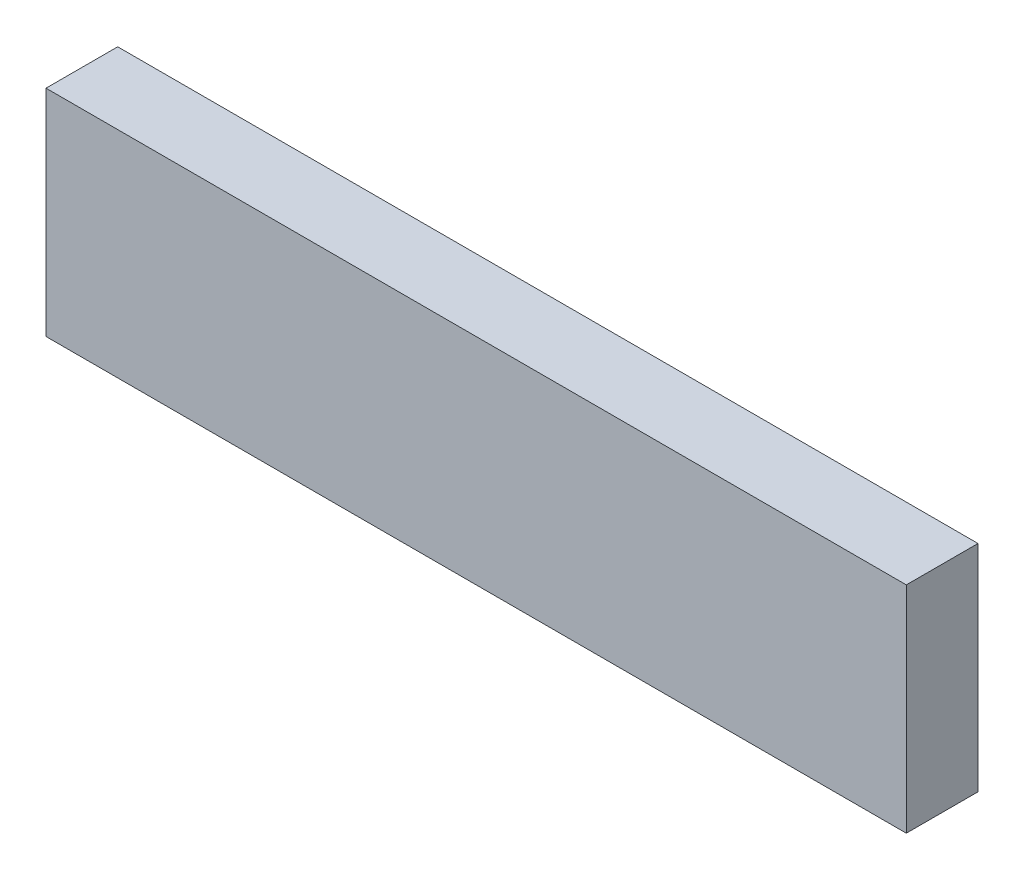
SolidWorks part; units mm, degrees
ref_plane "Front Plane" through (0, 0, 0) normal (0, 0, 1) x (1, 0, 0)
ref_plane "Top Plane" through (0, 0, 0) normal (0, 1, 0) x (1, 0, 0)
ref_plane "Right Plane" through (0, 0, 0) normal (1, 0, 0) x (0, 0, -1)
sketch "Sketch1" plane through (0, 0, 0) normal (0, 0, 1) x (1, 0, 0)
  line L1 (0, 0) -> (60, 0)
  line L2 (0, 0) -> (0, 15)
  line L3 (0, 15) -> (60, 15)
  line L4 (60, 0) -> (60, 15)
  dimension "D1" = 15
  dimension "D2" = 60
extrude "Boss-Extrude1" add sketch "Sketch1" along normal blind 5
